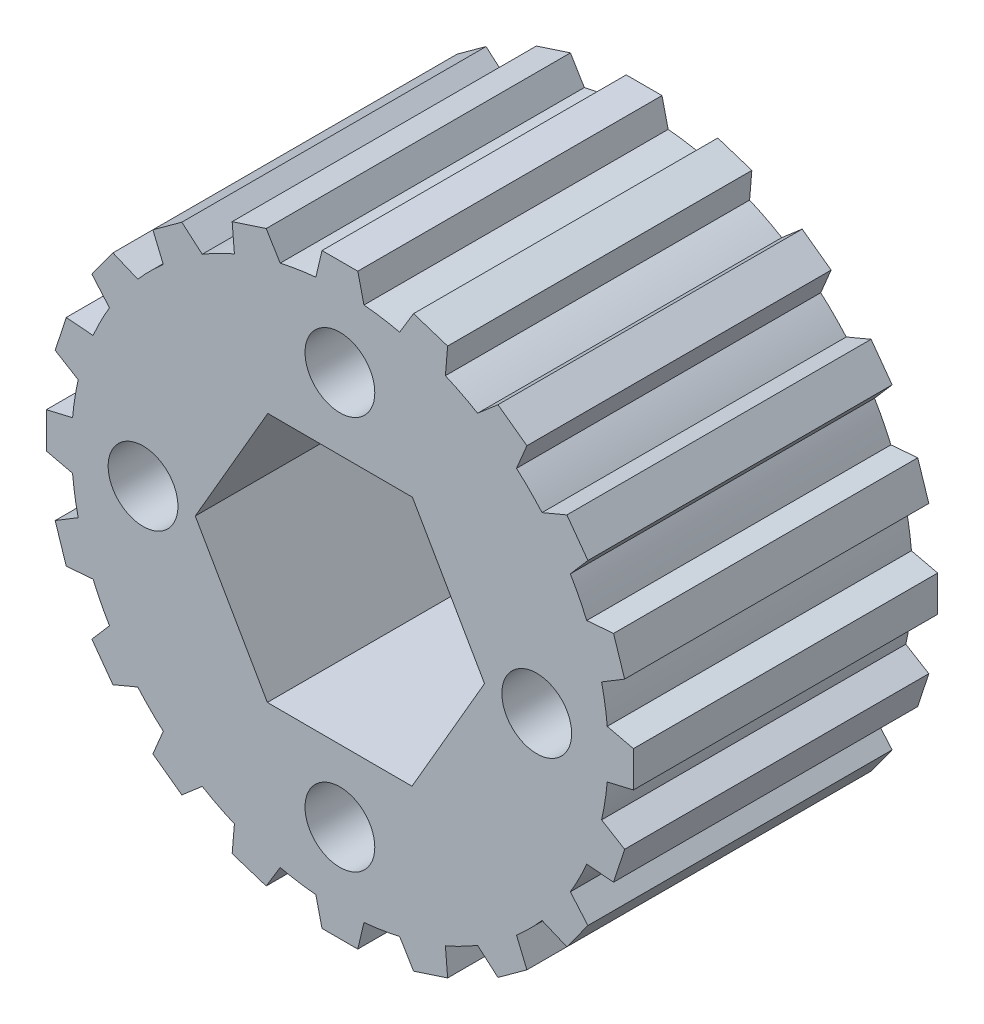
SolidWorks part; units mm, degrees
ref_plane "Front Plane" through (0, 0, 0) normal (0, 0, 1) x (1, 0, 0)
ref_plane "Top Plane" through (0, 0, 0) normal (0, 1, 0) x (1, 0, 0)
ref_plane "Right Plane" through (0, 0, 0) normal (1, 0, 0) x (0, 0, -1)
sketch "Sketch1" plane through (0, 0, 0) normal (0, 0, 1) x (1, 0, 0)
  circle A0 centre (0, 0) radius 15
  dimension "D1" = 30
extrude "Extrude1" add sketch "Sketch1" along normal blind 17
sketch "Sketch2" plane through (0, 0, 17) normal (0, 0, 1) x (1, 0, 0)
  line L0 (1.4, 14.7045) -> (1, 16.4045)
  line L1 (1, 16.4045) -> (-1, 16.4045)
  line L2 (-1, 16.4045) -> (-1.4, 14.7045)
  line L3 (-1.4, 14.7045) -> (1.4, 14.7045)
  line L4 (0, 0) -> (0, 39.164) construction
  point P7 (0, 14.7045)
  point P8 (0, 16.4045)
  dimension "D1" = 2.8
  dimension "D2" = 2
  dimension "D3" = 1.7
extrude "Extrude3" add sketch "Sketch2" against normal up to surface (17 mm away) up to face at (15, 0, 0)
pattern_circular "CirPattern1" count 20 every 18 about axis through (0, 0, 0) along (0, 0, 1) of "Extrude3"
hole_wizard "Ø8.2 (8.2) Diameter Hole1" positions "3DSketch1" profile "Sketch3" hole size "Ø8.2" standard "Ansi Metric"
sketch3d "3DSketch1"
  point P4 (0, 0, 0)
sketch "Sketch3" plane through (0, 0, 0) normal (1, 0, 0) x (0, 1, 0)
  line L0 (0, 0) -> (0, 12.4635)
  line L1 (0, 12.4635) -> (4.1, 10)
  line L2 (4.1, 10) -> (4.1, 0)
  line L5 (4.1, 0) -> (0, 0)
  line L10 (0, 12.4635) -> (-4.1, 10) construction
  line L11 (0, -6.35) -> (0, 107.95) construction
  dimension "Hole Dia." = 8.2
  dimension "Hole Depth" = 10
  dimension "Drill Angle" = 118
sketch "Sketch6" plane through (0, 0, 17) normal (0, 0, 1) x (1, 0, 0)
  line L1 (4.0538, 6.9929) -> (-4.0291, 7.0071)
  line L2 (-4.0291, 7.0071) -> (-8.0829, 0.0142)
  line L3 (-8.0829, 0.0142) -> (-4.0538, -6.9929)
  line L4 (-4.0538, -6.9929) -> (4.0291, -7.0071)
  line L5 (4.0291, -7.0071) -> (8.0829, -0.0142)
  line L6 (8.0829, -0.0142) -> (4.0538, 6.9929)
  circle A1 centre (0, 0) radius 7 construction
  dimension "D1" = 14
extrude "Extrude5" cut sketch "Sketch6" against normal blind 14
sketch "Sketch7" plane through (0, 0, 17) normal (0, 0, 1) x (1, 0, 0)
  line L2 (-16.2807, 0) -> (0, 0) construction
  circle A0 centre (-11, 0) radius 1.95
  circle A1 centre (0, 11) radius 1.95
  circle A2 centre (11, 0) radius 1.95
  circle A3 centre (0, -11) radius 1.95
  dimension "D3" = 3.9
  dimension "D2" = 11
extrude "Extrude6" cut sketch "Sketch7" against normal blind 15
